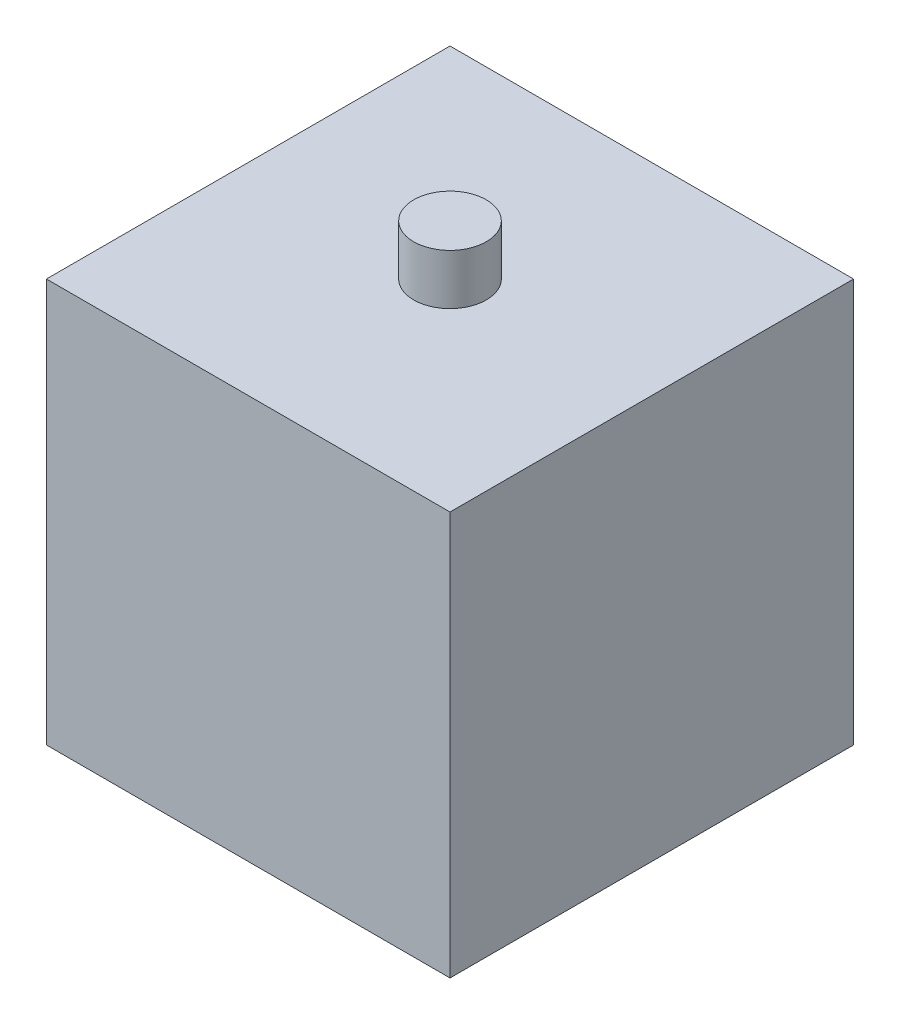
SolidWorks part; units mm, degrees
material "Plain Carbon Steel"
ref_plane "Front Plane" through (0, 0, 0) normal (0, 0, 1) x (1, 0, 0)
ref_plane "Top Plane" through (0, 0, 0) normal (0, 1, 0) x (1, 0, 0)
ref_plane "Right Plane" through (0, 0, 0) normal (1, 0, 0) x (0, 0, -1)
sketch "Sketch1" plane through (0, 0, 0) normal (0, 1, 0) x (1, 0, 0)
  line L1 (-12.7, -12.7) -> (12.7, -12.7)
  line L2 (-12.7, -12.7) -> (-12.7, 12.7)
  line L3 (-12.7, 12.7) -> (12.7, 12.7)
  line L4 (12.7, -12.7) -> (12.7, 12.7)
  line L5 (-12.7, -12.7) -> (12.7, 12.7) construction
  line L6 (-12.7, 12.7) -> (12.7, -12.7) construction
  point P0 (0, 0)
  dimension "D1" = 25.4
extrude "Boss-Extrude1" add sketch "Sketch1" along normal mid plane 25.4 contours L2 L3 L4 L1
sketch "Sketch2" plane through (0, 12.7, 0) normal (0, 1, 0) x (1, 0, 0)
  circle A0 centre (0, 0) radius 2.286
  dimension "D1" = 4.572
extrude "Boss-Extrude2" add sketch "Sketch2" along normal blind 3.175 contours A0
